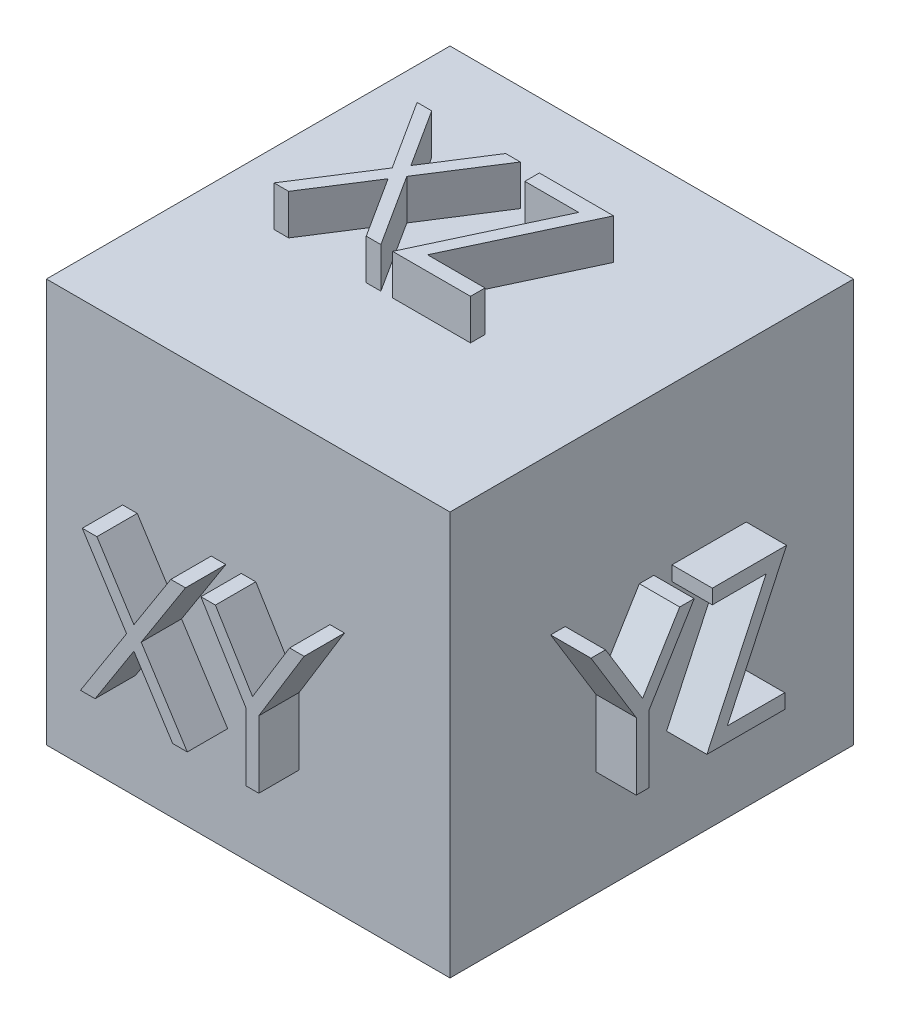
SolidWorks part; units mm, degrees
ref_plane "Front Plane" through (0, 0, 0) normal (0, 0, 1) x (1, 0, 0)
ref_plane "Top Plane" through (0, 0, 0) normal (0, 1, 0) x (1, 0, 0)
ref_plane "Right Plane" through (0, 0, 0) normal (1, 0, 0) x (0, 0, -1)
sketch "Sketch1" plane through (0, 0, 0) normal (0, 1, 0) x (1, 0, 0)
  line L1 (0, 0) -> (10, 0)
  line L2 (0, 0) -> (0, 10)
  line L3 (0, 10) -> (10, 10)
  line L4 (10, 0) -> (10, 10)
  dimension "D1" = 10
  dimension "D2" = 10
extrude "Boss-Extrude1" add sketch "Sketch1" along normal blind 10
sketch "Sketch2" plane through (0, 0, 0) normal (0, 0, 1) x (1, 0, 0)
  text T0 "XY\r\n"
  point P1 (1.6862, 2.5958)
  point P2 (0, 0)
  point P3 (0, 0)
extrude "Boss-Extrude2" add sketch "Sketch2" along normal blind 1
sketch "Sketch3" plane through (0, 10, 0) normal (0, 1, 0) x (1, 0, 0)
  text T0 "XZ\r\n"
extrude "Boss-Extrude3" add sketch "Sketch3" along normal blind 1
sketch "Sketch4" plane through (10, 0, 0) normal (1, 0, 0) x (0, 0, -1)
  text T0 "YZ\r\n"
  point P1 (2.3144, 2.6158)
extrude "Boss-Extrude4" add sketch "Sketch4" along normal blind 1
